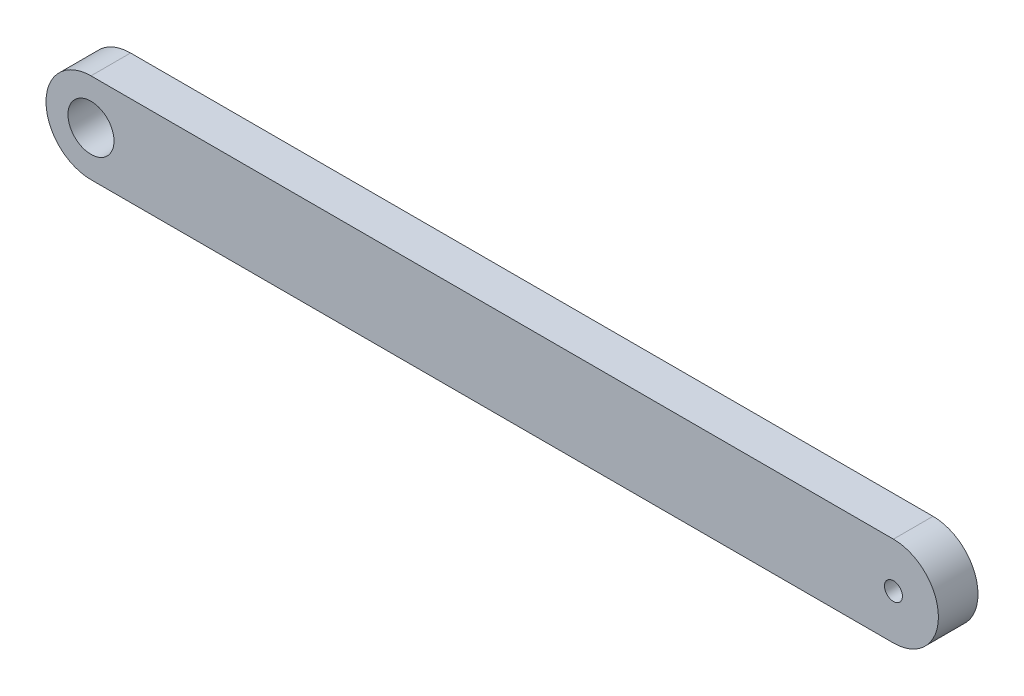
SolidWorks part; units mm, degrees
ref_plane "Front Plane" through (0, 0, 0) normal (0, 0, 1) x (1, 0, 0)
ref_plane "Top Plane" through (0, 0, 0) normal (0, 1, 0) x (1, 0, 0)
ref_plane "Right Plane" through (0, 0, 0) normal (1, 0, 0) x (0, 0, -1)
sketch "Sketch1" plane through (0, 0, 0) normal (0, 0, 1) x (1, 0, 0)
  line L0 (0, 0) -> (55.75, 0) construction
  line L1 (0, 3.125) -> (55.75, 3.125)
  line L2 (0, -3.125) -> (55.75, -3.125)
  arc A0 (0, 3.125) -> (0, -3.125) centre (0, 0) ccw
  arc A1 (55.75, -3.125) -> (55.75, 3.125) centre (55.75, 0) ccw
  circle A2 centre (0, 0) radius 1.6
  circle A3 centre (55.75, 0) radius 0.625
  point P3 (27.875, 0)
  dimension "D2" = 3.2
  dimension "D3" = 3.125
  dimension "D4" = 1.25
  dimension "D1" = 55.75
extrude "Boss-Extrude1" add sketch "Sketch1" along normal blind 2.75 contours L1 A1 L2 A0
